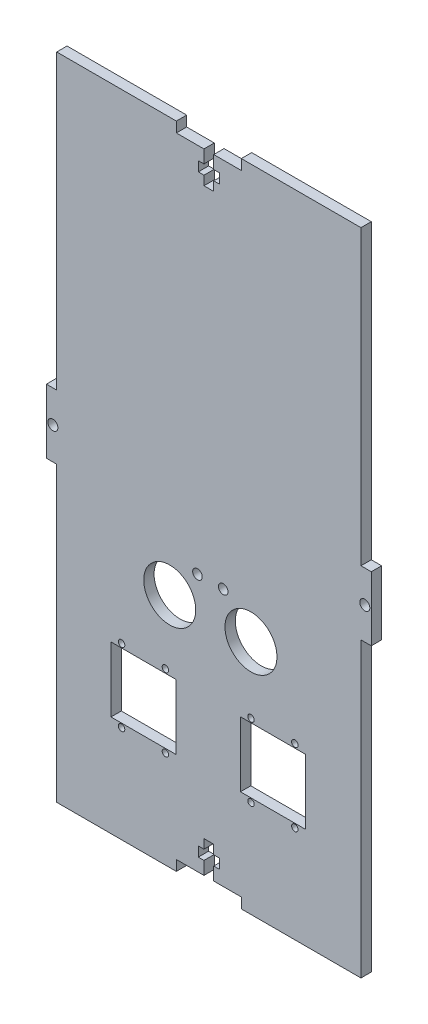
SolidWorks part; units mm, degrees
ref_plane "Front Plane" through (0, 0, 0) normal (0, 0, 1) x (1, 0, 0)
ref_plane "Top Plane" through (0, 0, 0) normal (0, 1, 0) x (1, 0, 0)
ref_plane "Right Plane" through (0, 0, 0) normal (1, 0, 0) x (0, 0, -1)
sketch "Sketch1" plane through (0, 0, 0) normal (0, 0, 1) x (1, 0, 0)
  line L0 (0.1756, 148.1163) -> (0.1756, -143.3274) construction
  line L5 (-50, -100) -> (50, 100) construction
  line L6 (-50, 100) -> (50, -100) construction
  line L7 (-100, 0) -> (100, 0) construction
  line L32 (-50, 100) -> (50, 100)
  line L35 (50, 100) -> (50, -100)
  line L36 (50, -100) -> (-50, -100)
  line L37 (-50, -100) -> (-50, 100)
  point P0 (0, 0)
  dimension "D1" = 100
  dimension "D2" = 200
extrude "Boss-Extrude2" add sketch "Sketch1" along normal blind 3.18
sketch "Sketch2" plane through (0, 0, 3.18) normal (0, 0, 1) x (1, 0, 0)
  line L0 (0, -100) -> (0, 100) construction
  line L1 (-123.0225, 0) -> (147.0753, 0) construction
  line L2 (50, 100) -> (-50, 100) construction
  line L4 (-10, 100) -> (-10, 96.82)
  line L5 (-10, 96.82) -> (-1.5, 96.82)
  line L6 (10, 100) -> (10, 96.82)
  line L7 (1.5, 96.82) -> (10, 96.82)
  line L9 (-1.5, 96.82) -> (-1.5, 92.82)
  line L10 (-1.5, 87) -> (1.5, 87)
  line L11 (1.5, 96.82) -> (1.5, 92.82)
  line L12 (-3.25, 92.82) -> (-1.5, 92.82)
  line L13 (-3.25, 92.82) -> (-3.25, 89.82)
  line L14 (-3.25, 89.82) -> (-1.5, 89.82)
  line L15 (3.25, 92.82) -> (3.25, 89.82)
  line L16 (1.5, 92.82) -> (3.25, 92.82)
  line L17 (-1.5, 89.82) -> (-1.5, 87)
  line L18 (1.5, 89.82) -> (1.5, 87)
  line L19 (1.5, 89.82) -> (3.25, 89.82)
  line L20 (-10, 100) -> (10, 100)
  line L21 (-50, -100) -> (50, -100) construction
  line L22 (-50, 100) -> (-50, -100) construction
  line L23 (-50, 9.875) -> (-46.82, 9.875)
  line L24 (-50, 9.875) -> (-50, 100)
  line L25 (-50, 100) -> (-46.82, 100)
  line L26 (-46.82, 9.875) -> (-46.82, 100)
  line L28 (-50, -9.875) -> (-46.82, -9.875)
  line L29 (-50, -9.875) -> (-50, -100)
  line L30 (-50, -100) -> (-46.82, -100)
  line L31 (-46.82, -9.875) -> (-46.82, -100)
  circle A0 centre (-48, 0) radius 1.55
  dimension "D11" = 3.1
  dimension "D12" = 2
  dimension "D1" = 4
  dimension "D2" = 3
  dimension "D3" = 3
  dimension "D4" = 20
  dimension "D5" = 6.5
  dimension "D6" = 3.18
  dimension "D7" = 13
  dimension "D8" = 19.75
  dimension "D9" = 3.18
  dimension "D10" = 3.18
extrude "Cut-Extrude1" cut sketch "Sketch2" against normal through all
mirror "Mirror1" about plane through (0, 0, 0) normal (0, 1, 0) of "Cut-Extrude1"
mirror "Mirror3" about plane through (0, 0, 0) normal (1, 0, 0) of "Cut-Extrude1"
sketch "Sketch4" plane through (0, 0, 0) normal (0, 0, -1) x (-1, 0, 0)
  circle A1 centre (13.3617, -70.1191) radius 1
  circle A2 centre (13.3617, -70.1191) radius 0.975 construction
  circle A3 centre (26.8617, -70.1191) radius 1
  circle A7 centre (26.8617, -70.1191) radius 0.975 construction
  circle A8 centre (26.8617, -47.6591) radius 1
  circle A9 centre (26.8617, -47.6591) radius 0.975 construction
  circle A10 centre (13.3617, -47.6591) radius 1
  circle A11 centre (13.3617, -47.6591) radius 0.975 construction
  circle A12 centre (-12.9789, -47.6824) radius 1
  circle A13 centre (-26.4789, -47.6824) radius 1
  circle A14 centre (-26.4789, -70.1424) radius 1
  circle A15 centre (-12.9789, -70.1424) radius 1
  circle A16 centre (-26.4789, -70.1424) radius 0.975 construction
  circle A17 centre (-12.9789, -70.1424) radius 0.975 construction
  circle A18 centre (-26.4789, -47.6824) radius 0.975 construction
  circle A19 centre (-12.9789, -47.6824) radius 0.975 construction
  dimension "D2" = 2
extrude "Cut-Extrude15" cut sketch "Sketch4" against normal blind 10
sketch "Sketch5" plane through (0, 0, 0) normal (0, 0, -1) x (-1, 0, 0)
  circle A0 centre (12.0316, -27.3421) radius 8
  circle A1 centre (-12.9684, -27.3421) radius 8
  circle A2 centre (12.0316, -27.3421) radius 8 construction
  circle A3 centre (-12.9684, -27.3421) radius 8 construction
  dimension "D1" = 16
extrude "Cut-Extrude16" cut sketch "Sketch5" against normal through all
sketch "Sketch6" plane through (0, 0, 0) normal (0, 0, -1) x (-1, 0, 0)
  circle A0 centre (3.4951, -17.5376) radius 1.47
  circle A2 centre (-4.4319, -17.5376) radius 1.47
  circle A3 centre (3.4951, -17.5376) radius 1.47 construction
  circle A4 centre (-4.4319, -17.5376) radius 1.47 construction
extrude "Cut-Extrude17" cut sketch "Sketch6" against normal through all
sketch "Sketch7" plane through (0, 0, 0) normal (0, 0, -1) x (-1, 0, 0)
  line L1 (30.1117, -48.8891) -> (10.1117, -48.8891)
  line L2 (30.1117, -48.8891) -> (30.1117, -68.8891)
  line L3 (30.1117, -68.8891) -> (10.1117, -68.8891)
  line L4 (10.1117, -48.8891) -> (10.1117, -68.8891)
  line L5 (-9.7289, -48.9124) -> (-29.7289, -48.9124)
  line L6 (-9.7289, -48.9124) -> (-9.7289, -68.9124)
  line L7 (-9.7289, -68.9124) -> (-29.7289, -68.9124)
  line L8 (-29.7289, -48.9124) -> (-29.7289, -68.9124)
  dimension "D1" = 20
extrude "Cut-Extrude18" cut sketch "Sketch7" against normal through all contours L2 L1 L4 L3 | L6 L5 L8 L7
